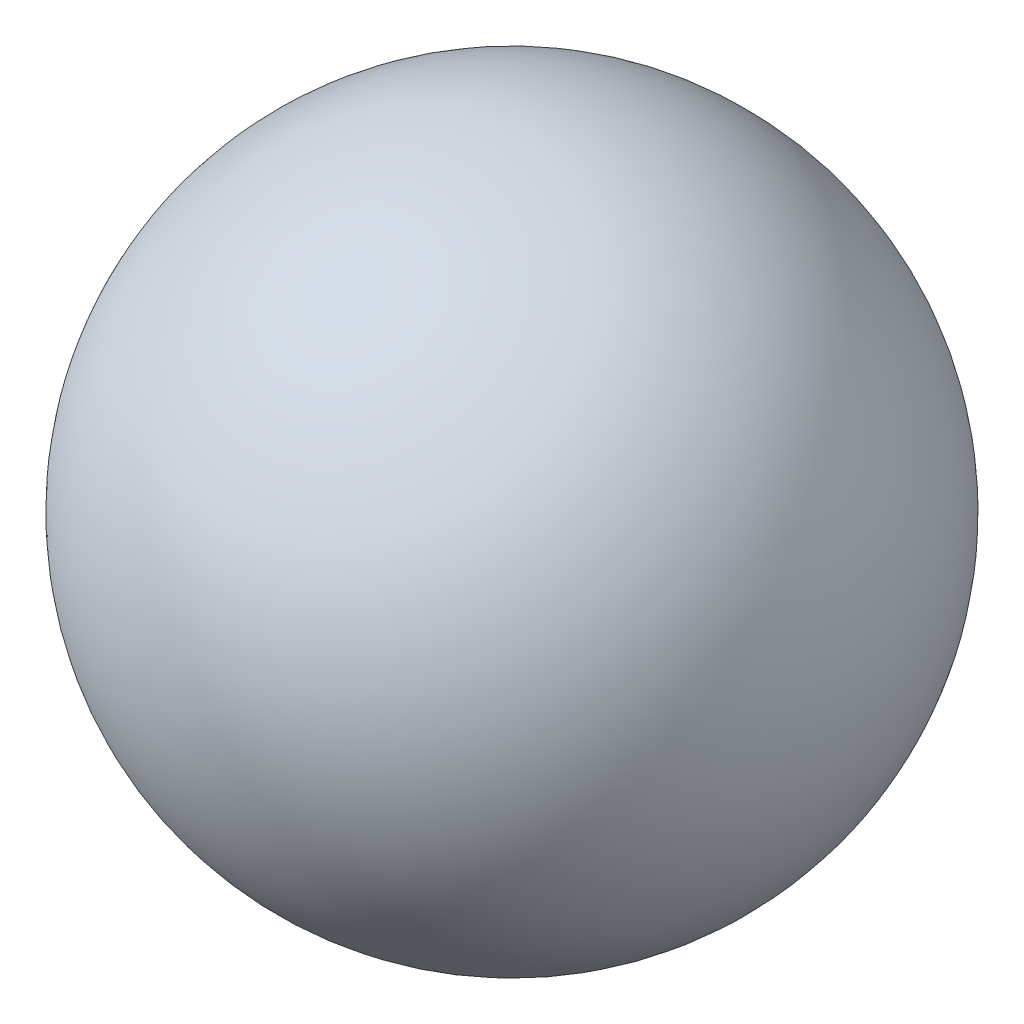
SolidWorks part; units mm, degrees
ref_plane "Ebene vorne" through (0, 0, 0) normal (0, 0, 1) x (1, 0, 0)
ref_plane "Ebene oben" through (0, 0, 0) normal (0, 1, 0) x (1, 0, 0)
ref_plane "Ebene rechts" through (0, 0, 0) normal (1, 0, 0) x (0, 0, -1)
ref_plane "Ebene1" through (0, 0, 0) normal (0, 0, 1) x (1, 0, 0)
sketch "Skizze1" plane through (0, 0, 0) normal (0, 0, 1) x (1, 0, 0)
  line L0 (5.4845, 7.35) -> (1.5155, 7.35)
  line L1 (5.4845, 7.35) -> (1.5155, 7.35) construction
  arc A0 (1.5155, 7.35) -> (5.4845, 7.35) centre (3.5, 7.35) cw
revolve "Rotation1" add sketch "Skizze1" angle 360 about L1
